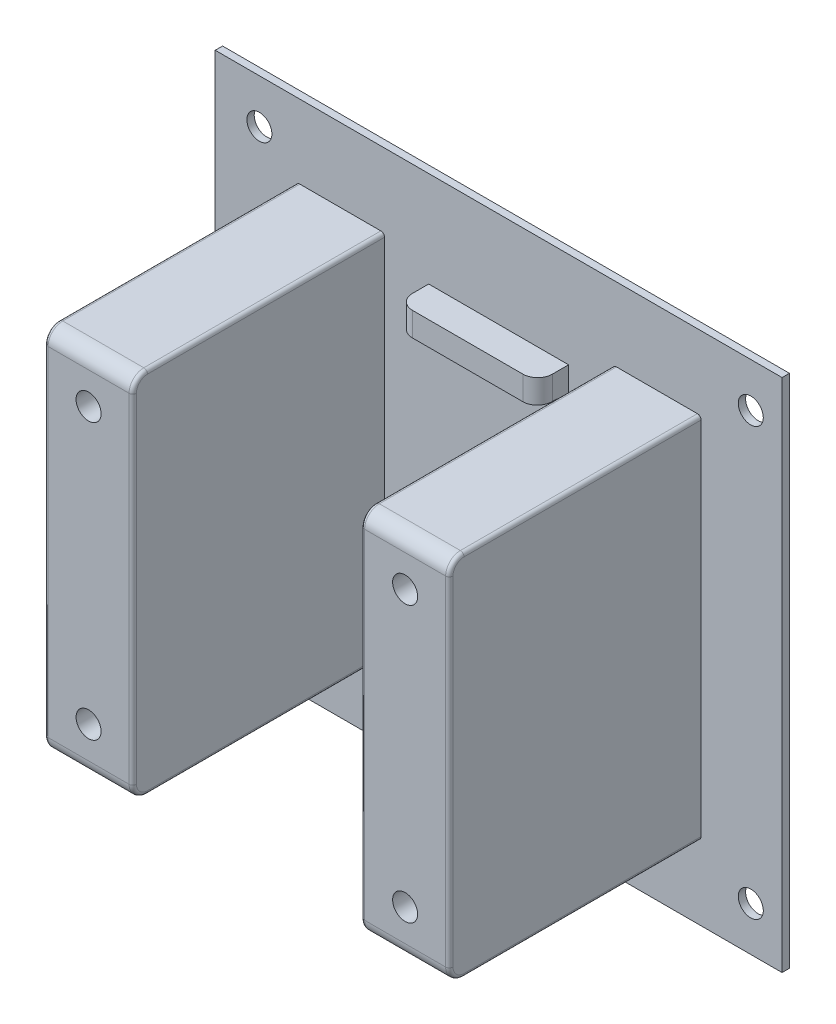
SolidWorks part; units mm, degrees
ref_plane "Front Plane" through (0, 0, 0) normal (1, 0, 0) x (0, 1, 0)
ref_plane "Bottom Plane" through (0, 0, 0) normal (0, 0, 1) x (0, 1, 0)
ref_plane "Right Plane" through (0, 0, 0) normal (0, 1, 0) x (-1, 0, 0)
ref_plane "Base Cut" through (0, 0, 7) normal (0, 0, 1) x (0, 1, 0)
sketch "Structural screws w/o heads" plane through (0, 0, 0) normal (0, 0, 1) x (0, 1, 0)
  line L1 (-19.42, -19.42) -> (19.42, -19.42) construction
  line L2 (-19.42, -19.42) -> (-19.42, 19.42) construction
  line L3 (-19.42, 19.42) -> (19.42, 19.42) construction
  line L4 (19.42, -19.42) -> (19.42, 19.42) construction
  line L5 (-19.42, -19.42) -> (19.42, 19.42) construction
  line L6 (-19.42, 19.42) -> (19.42, -19.42) construction
  circle A0 centre (-19.42, 19.42) radius 1.65 construction
  circle A1 centre (-19.42, -19.42) radius 1.65 construction
  circle A2 centre (19.42, 19.42) radius 1.65 construction
  circle A3 centre (19.42, -19.42) radius 1.65 construction
  circle A4 centre (0, 10.32) radius 1.65 construction
  circle A5 centre (0, -10.32) radius 1.65 construction
  point P0 (0, 0)
  dimension "D3" = 3.3
  dimension "D4" = 3.3
  dimension "D5" = 3.3
  dimension "D6" = 3.3
  dimension "D7" = 3.3
  dimension "D8" = 10.32
  dimension "D9" = 3.3
  dimension "D10" = 10.32
  dimension "D11" = 9.1
  dimension "D12" = 9.1
  dimension "D1" = 38.84
  dimension "D2" = 38.84
sketch "Sketch6" plane through (0, 0, 0) normal (0, 0, 1) x (0, 1, 0)
  line L0 (-30, -26.5) -> (-30, -31.5)
  line L1 (-30, 26.5) -> (30, 26.5)
  line L2 (-30, 26.5) -> (-30, -26.5)
  line L4 (30, 26.5) -> (30, -26.5)
  line L5 (-30, 26.5) -> (30, -26.5) construction
  line L6 (-30, -26.5) -> (30, 26.5) construction
  line L7 (30, -26.5) -> (30, -31.5)
  line L8 (-30, -31.5) -> (30, -31.5)
  point P0 (0, 0)
  dimension "D1" = 60
  dimension "D2" = 53
  dimension "D3" = 5
  dimension "D4" = 53
extrude "Mount Base" add sketch "Sketch6" along normal blind 10 separate body
sketch "Sketch 8" plane through (0, 0, 7) normal (0, 0, 1) x (0, 1, 0)
  line L1 (-19, 15.5) -> (19, 15.5)
  line L2 (-19, 15.5) -> (-19, -15.5)
  line L3 (-19, -15.5) -> (19, -15.5)
  line L4 (19, 15.5) -> (19, -15.5)
  line L5 (-19, 15.5) -> (19, -15.5) construction
  line L6 (-19, -15.5) -> (19, 15.5) construction
  point P0 (0, 0)
  dimension "D1" = 38
  dimension "D2" = 31
extrude "Cut-Base" cut sketch "Sketch 8" along normal blind 34
ref_plane "Bend Surface Plane" through (0, 0, 10) normal (0, 0, 1) x (0, 1, 0)
sketch "Sketch10" plane through (0, 0, 10) normal (0, 0, 1) x (0, 1, 0)
  line L0 (19, 0) -> (-19, 0) construction
  line L1 (-19, -15.5) -> (-19, 15.5) construction
  line L2 (0, 15.5) -> (0, -15.5) construction
  line L3 (-19, 15.5) -> (-22, 15.5)
  line L4 (-19, 15.5) -> (-19, -15.5)
  line L5 (-19, -15.5) -> (-22, -15.5)
  line L6 (-22, 15.5) -> (-22, -15.5)
  line L7 (19, -15.5) -> (-19, -15.5) construction
  line L8 (19, -15.5) -> (22, -15.5)
  line L9 (22, 15.5) -> (22, -15.5)
  line L10 (19, 15.5) -> (22, 15.5)
  line L11 (19, 15.5) -> (19, -15.5)
  point P6 (0, 0)
  point P17 (0, 0)
  dimension "D1" = 31
  dimension "D2" = 3
extrude "Bend Sides" add sketch "Sketch10" along normal blind 34.2
sketch "E-stop" plane through (0, 0, 10) normal (0, 0, 1) x (0, 1, 0)
  line L1 (-18.195, 14.995) -> (18.195, 14.995)
  line L2 (-18.195, 14.995) -> (-18.195, -14.995)
  line L3 (-18.195, -14.995) -> (18.195, -14.995)
  line L4 (18.195, 14.995) -> (18.195, -14.995)
  line L5 (-18.195, 14.995) -> (18.195, -14.995) construction
  line L6 (-18.195, -14.995) -> (18.195, 14.995) construction
  point P0 (0, 0)
  dimension "D1" = 36.39
  dimension "D2" = 29.99
ref_plane "Plane6" through (0, 0, 44.2) normal (0, 0, 1) x (1, 0, 0)
sketch "Sketch16" plane through (0, 0, 10) normal (0, 0, 1) x (0, 1, 0)
  line L0 (-22, 0) -> (22, 0) construction
  line L1 (-22, -15.5) -> (22, -15.5)
  line L2 (-22, -15.5) -> (-22, -18.5)
  line L3 (-22, -18.5) -> (22, -18.5)
  line L4 (22, -15.5) -> (22, -18.5)
  line L5 (22, -15.5) -> (22, 15.5) construction
  line L6 (-22, 18.5) -> (22, 18.5)
  line L7 (22, 15.5) -> (22, 18.5)
  line L8 (-22, 15.5) -> (22, 15.5)
  line L9 (-22, 15.5) -> (-22, 18.5)
  point P11 (0, 0)
  dimension "D1" = 44
  dimension "D2" = 3
extrude "Wire Sides" add sketch "Sketch16" along normal blind 34.2
ref_plane "Wire Holes Plane" through (0, 0, 44.2) normal (0, 0, 1) x (1, 0, 0)
draft "Draft9" type of draft neutral plane draft angle 1 faces to draft 1 face at (0, -19, 25.6) neutral plane through (0, 0, 0) neutral plane normal (0, 0, -1) parameters "D1"=1
draft "Draft10" type of draft neutral plane draft angle 1 faces to draft 1 face at (0, 19, 25.6) neutral plane through (0, 0, 0) neutral plane normal (0, 0, -1) parameters "D1"=1
sketch "Sketch20" plane through (0, 0, 0) normal (0, 0, 1) x (0, 1, 0)
  line L0 (0, 0) -> (0, 25) construction
  line L2 (-30, 26.5) -> (-30, 37)
  line L3 (-30, 37) -> (30, 37)
  line L4 (30, 27) -> (30, 37)
  line L5 (-30, 0) -> (30, 0) construction
  line L10 (0, 30.5) -> (0, -30.5) construction
  line L11 (0, -30.5) -> (-30, -28.4968) construction
  line L12 (0, -30.5) -> (30, -28.4968) construction
  line L13 (0, 30.5) -> (30, 28.4968) construction
  line L14 (0, 30.5) -> (-30, 28.4968) construction
  line L15 (-30, -37) -> (30, -37)
  line L16 (30, 27) -> (30, -37)
  line L18 (-30, 26.5) -> (-30, -37)
  point P11 (0, 0)
  point P19 (0, 0)
  dimension "D1" = 10
  dimension "D2" = 60
  dimension "D3" = 37
  dimension "D4" = 30.0668
  dimension "D5" = 30.4322
  dimension "D6" = 172.36
ref_plane "Plane8" through (0, 0, -3.18) normal (0, 0, 1) x (0, 1, 0)
extrude "Differential Clamp" add sketch "Sketch20" against normal blind 8.6 and the other way blind 10
sketch "Sketch22" plane through (0, 0, 0) normal (0, 0, 1) x (0, 1, 0)
  line L2 (-86.9562, -24.6938) -> (0, -30.5)
  line L7 (-30, 37) -> (30, 37)
  line L9 (-30, 37) -> (-86.9562, 37)
  line L10 (-86.9562, 37) -> (-86.9562, -24.6938)
  line L11 (0, -30.5) -> (0, 37) construction
  line L12 (86.9562, -24.6938) -> (0, -30.5)
  line L13 (30, 37) -> (86.9562, 37)
  line L14 (86.9562, 37) -> (86.9562, -24.6938)
  point P20 (0, 0)
  dimension "D1" = 61.6938
  dimension "D2" = 87.1498
extrude "Differential Bar cut" cut sketch "Sketch22" against normal blind 3.6 contours L2 L12 L14 L13 L7 L9 L10
ref_plane "Plane9" through (0, 0, -8.6) normal (0, 0, -1) x (-1, 0, 0)
sketch "Sketch 7" plane through (0, 0, 0) normal (0, 0, 1) x (0, 1, 0)
  line L0 (-22.42, 37.1638) -> (-22.42, -19.42)
  line L2 (-22.42, 37.1638) -> (-16.42, 37.1638)
  line L3 (-16.42, 37.1638) -> (-16.42, -19.42)
  line L4 (16.42, -19.42) -> (16.42, 37.1612)
  line L5 (-3, 37.1612) -> (3, 37.1612)
  line L6 (22.42, 37.1612) -> (22.42, -19.42)
  line L11 (-3, -10.32) -> (-3, 37.1612)
  line L12 (3, -10.32) -> (3, 37.1612)
  line L13 (16.42, 37.1612) -> (22.42, 37.1612)
  arc A1 (-22.42, -19.42) -> (-16.42, -19.42) centre (-19.42, -19.42) ccw
  arc A3 (16.42, -19.42) -> (22.42, -19.42) centre (19.42, -19.42) ccw
  arc A5 (-3, -10.32) -> (3, -10.32) centre (0, -10.32) ccw
  dimension "D1" = 56.5838
  dimension "D2" = 6
  dimension "D3" = 6
  dimension "D4" = 56.5812
  dimension "D5" = 6
  dimension "D6" = 6
  dimension "D7" = 6
  dimension "D8" = 44.84
extrude "Structural Screw w/ heads" cut sketch "Sketch 7" along normal blind 5
ref_plane "Clamp Hole Plane" through (0, 0, 10) normal (0, 0, 1) x (0, 1, 0)
sketch "Sketch25" plane through (0, 0, 10) normal (0, 0, 1) x (1, 0, 0)
  line L0 (-37, -30) -> (-37, 30) construction
  line L1 (37, 30) -> (-37, 30) construction
  line L2 (37, 0) -> (-37, 0) construction
  line L3 (0, 30) -> (0, -30) construction
  line L4 (-37, -30) -> (37, -30) construction
  circle A0 centre (-32, 29) radius 1.7
  circle A1 centre (-32, -29) radius 1.7
  circle A2 centre (32, -29) radius 1.7
  circle A3 centre (32, 29) radius 1.7
  point P10 (0, 0)
  point P17 (0, 0)
  dimension "D1" = 3.4
  dimension "D2" = 5
  dimension "D3" = 1
extrude "Screw holes" cut sketch "Sketch25" against normal blind 24
ref_plane "Plane11" through (0, 0, -8.6) normal (0, 0, -1) x (-1, 0, 0)
sketch "Sketch27" plane through (0, 0, -8.6) normal (0, 0, -1) x (-1, 0, 0)
  line L0 (37, -30) -> (37, 30) construction
  line L1 (31.9351, 25.7097) -> (34.817, 27.2987)
  line L2 (34.817, 27.2987) -> (34.8819, 30.5889)
  line L3 (34.8819, 30.5889) -> (32.0649, 32.2903)
  line L4 (32.0649, 32.2903) -> (29.183, 30.7013)
  line L5 (29.183, 30.7013) -> (29.1181, 27.4111)
  line L6 (29.1181, 27.4111) -> (31.9351, 25.7097)
  line L7 (-37, -30) -> (-33.3748, -30) construction
  line L8 (28.7091, -29) -> (30.3546, -31.85)
  line L9 (30.3546, -31.85) -> (33.6454, -31.85)
  line L10 (33.6454, -31.85) -> (35.2909, -29)
  line L11 (35.2909, -29) -> (33.6454, -26.15)
  line L12 (33.6454, -26.15) -> (30.3546, -26.15)
  line L13 (30.3546, -26.15) -> (28.7091, -29)
  line L14 (0, 30) -> (0, -30) construction
  line L15 (-30.3546, -26.15) -> (-28.7091, -29)
  line L16 (-33.6454, -26.15) -> (-30.3546, -26.15)
  line L17 (-35.2909, -29) -> (-33.6454, -26.15)
  line L18 (-33.6454, -31.85) -> (-35.2909, -29)
  line L19 (-30.3546, -31.85) -> (-33.6454, -31.85)
  line L20 (-28.7091, -29) -> (-30.3546, -31.85)
  line L21 (-29.1181, 27.4111) -> (-31.9351, 25.7097)
  line L22 (-29.183, 30.7013) -> (-29.1181, 27.4111)
  line L23 (-32.0649, 32.2903) -> (-29.183, 30.7013)
  line L24 (-34.8819, 30.5889) -> (-32.0649, 32.2903)
  line L25 (-34.817, 27.2987) -> (-34.8819, 30.5889)
  line L26 (-31.9351, 25.7097) -> (-34.817, 27.2987)
  circle A0 centre (32, 29) radius 2.85 construction
  circle A1 centre (32, -29) radius 2.85 construction
  circle A2 centre (-32, -29) radius 2.85 construction
  circle A3 centre (-32, 29) radius 2.85 construction
  point P26 (0, 0)
  dimension "D3" = 5.7
  dimension "D1" = 5.7
  dimension "D2" = 1.13
  dimension "D4" = 1
extrude "Nut hole" cut sketch "Sketch27" against normal blind 2.6
fillet "Fillet7" radius 2 1 edges at (-37, 30, 5)
fillet "Fillet8" radius 2 1 edges at (-37, -30, 5)
fillet "Fillet9" radius 2 1 edges at (-37, 30, -6.1)
fillet "Fillet10" radius 2 1 edges at (-37, -30, -6.1)
fillet "Fillet15" radius 2 2 edges at (0, 18.8254, 10) (0, -18.8254, 10)
ref_plane "Sectional Left Plane" through (0, 22, 0) normal (0, 1, 0) x (1, 0, 0)
ref_plane "Sectional Right Plane" through (0, -22, 0) normal (0, -1, 0) x (-1, 0, 0)
ref_plane "Plane13" through (0, 0, 9) normal (0, 0, 1) x (1, 0, 0)
sketch "Sketch41" plane through (0, 0, 9) normal (0, 0, 1) x (1, 0, 0)
  line L1 (37.5468, -30.066) -> (-37.5468, -30.066)
  line L2 (37.5468, -30.066) -> (37.5468, 30.066)
  line L3 (37.5468, 30.066) -> (-37.5468, 30.066)
  line L4 (-37.5468, -30.066) -> (-37.5468, 30.066)
  line L5 (37.5468, -30.066) -> (-37.5468, 30.066) construction
  line L6 (37.5468, 30.066) -> (-37.5468, -30.066) construction
  point P0 (0, 0)
  dimension "D1" = 60.132
  dimension "D2" = 75.0936
ref_plane "Plane15" through (0, 0, -8.6) normal (0, 0, -1) x (-1, 0, 0)
sketch "Sketch42" plane through (0, 0, -8.6) normal (0, 0, 1) x (1, 0, 0)
  line L0 (0, 23) -> (0, -23) construction
  line L1 (37, 35) -> (-37, 35)
  line L2 (37, 35) -> (37, -35)
  line L3 (37, -35) -> (-37, -35)
  line L4 (-37, 35) -> (-37, 23)
  line L5 (37, 35) -> (-37, -35) construction
  line L6 (37, -35) -> (-37, 35) construction
  line L7 (37, 0) -> (28.5, 0) construction
  line L8 (28.5, 23) -> (28.5, -23)
  line L9 (28.5, 23) -> (-37, 23)
  line L10 (28.5, -23) -> (-37, -23)
  line L11 (-37, -23) -> (-37, -35)
  point P0 (0, 0)
  point P9 (0, 0)
  point P14 (28.5, 0)
  point P17 (0, 23)
  point P20 (0, -23)
  dimension "D1" = 74
  dimension "D2" = 46
  dimension "D3" = 70
  dimension "D4" = 65.5
  dimension "D5" = 46
  dimension "D6" = 12
extrude "Boss-Extrude1" add sketch "Sketch42" along normal blind 17.6
ref_plane "Plane16" through (0, 0, 0) normal (0, 0, -1) x (-1, 0, 0)
sketch "Sketch43" plane through (0, 0, 0) normal (0, 0, -1) x (-1, 0, 0)
  line L0 (-24.6938, 86.9562) -> (37, 86.9562)
  line L1 (37, 86.9562) -> (37, -86.9562)
  line L2 (37, -86.9562) -> (-24.6938, -86.9562)
  line L3 (-24.6938, -86.9562) -> (-30.5, 0)
  line L4 (-30.5, 0) -> (-24.6938, 86.9562)
extrude "Cut-Extrude6" cut sketch "Sketch43" along normal blind 8.6
sketch "Sketch45" plane through (0, 0, 0) normal (0, 0, -1) x (-1, 0, 0)
  line L0 (37, 23) -> (-28.5, 23)
  line L1 (-28.5, 23) -> (-28.5, -23)
  line L2 (-28.5, -23) -> (37, -23)
  line L3 (37, -23) -> (37, 23)
ref_plane "Plane17" through (0, 0, -8.6) normal (0, 0, -1) x (-1, 0, 0)
ref_plane "Plane18" through (0, 0, 9) normal (0, 0, 1) x (1, 0, 0)
sketch "Sketch48" plane through (0, 0, 9) normal (0, 0, 1) x (1, 0, 0)
  line L1 (-37, 35) -> (37, 35)
  line L2 (-37, 35) -> (-37, -35)
  line L3 (-37, -35) -> (37, -35)
  line L4 (37, 35) -> (37, -35)
extrude "Cut-Extrude9" cut sketch "Sketch48" against normal blind 17.6
sketch "Sketch49" plane through (0, 0, 9) normal (0, 0, 1) x (1, 0, 0)
  line L1 (38.5, -35) -> (-38.5, -35)
  line L2 (38.5, -35) -> (38.5, 35)
  line L3 (38.5, 35) -> (-38.5, 35)
  line L4 (-38.5, -35) -> (-38.5, 35)
  line L5 (38.5, -35) -> (-38.5, 35) construction
  line L6 (38.5, 35) -> (-38.5, -35) construction
  point P0 (0, 0)
  dimension "D1" = 70
  dimension "D2" = 77
extrude "Boss-Extrude2" add sketch "Sketch49" along normal blind 1
sketch "Sketch50" plane through (0, 0, 9) normal (0, 0, 1) x (1, 0, 0)
  line L0 (-38.5, 29) -> (38.5, 29) construction
  line L1 (-38.5, 35) -> (-38.5, -35) construction
  line L2 (38.5, -35) -> (38.5, 35) construction
  line L3 (38.5, 35) -> (-38.5, 35) construction
  line L4 (37, 0) -> (-37, 0) construction
  line L5 (34.25, 29) -> (34.25, -29) construction
  line L7 (-32.5, 29) -> (-32.5, -29) construction
  line L8 (-38.5, -29) -> (38.5, -29) construction
  circle A0 centre (-32.5, 29) radius 1.7
  circle A1 centre (34.25, 29) radius 1.7
  circle A2 centre (34.25, -29) radius 1.7
  circle A3 centre (-32.5, -29) radius 1.7
  point P12 (0, 0)
  point P21 (34.25, 0)
  point P25 (-32.5, 0)
  dimension "D4" = 3.4
  dimension "D5" = 3.4
  dimension "D1" = 6
  dimension "D2" = 4.25
  dimension "D3" = 6
extrude "Cut-Extrude10" cut sketch "Sketch50" along normal blind 1
ref_plane "Plane20" through (0, 0, 10) normal (0, 0, 1) x (1, 0, 0)
ref_plane "Plane21" through (0, 0, 44.2) normal (0, 0, 1) x (1, 0, 0)
sketch "Sketch52" plane through (0, 0, 44.2) normal (0, 0, 1) x (1, 0, 0)
  line L0 (9.5, 0) -> (-9.5, 0) construction
  line L1 (15.5, 16.7902) -> (-15.5, 16.7902) construction
  line L3 (0, 8.1338) -> (0, -8.1338) construction
  line L13 (-15.5, 24.2285) -> (-9.5, 24.2285)
  line L16 (-9.5, 24.2285) -> (-9.5, 18.2285)
  line L29 (-15.5, 18.2285) -> (-15.5, 24.2285)
  line L31 (-18.5, 22) -> (-18.5, -22) construction
  line L55 (-15.5, 18.2285) -> (-15.5, 16.7902)
  line L56 (-15.5, 16.7902) -> (-9.5, 16.7902)
  line L57 (-9.5, 18.2285) -> (-9.5, 16.7902)
  line L58 (15.5, 18.2285) -> (15.5, 16.7902)
  line L59 (15.5, 16.7902) -> (9.5, 16.7902)
  line L60 (9.5, 18.2285) -> (9.5, 16.7902)
  line L61 (9.5, 24.2285) -> (9.5, 18.2285)
  line L62 (15.5, 24.2285) -> (9.5, 24.2285)
  line L63 (15.5, 18.2285) -> (15.5, 24.2285)
  line L64 (15.5, -18.2285) -> (15.5, -24.2285)
  line L65 (15.5, -24.2285) -> (9.5, -24.2285)
  line L66 (9.5, -24.2285) -> (9.5, -18.2285)
  line L67 (9.5, -18.2285) -> (9.5, -16.7902)
  line L68 (15.5, -16.7902) -> (9.5, -16.7902)
  line L69 (15.5, -18.2285) -> (15.5, -16.7902)
  line L70 (-15.5, -18.2285) -> (-15.5, -16.7902)
  line L71 (-15.5, -16.7902) -> (-9.5, -16.7902)
  line L72 (-9.5, -18.2285) -> (-9.5, -16.7902)
  line L73 (-9.5, -24.2285) -> (-9.5, -18.2285)
  line L74 (-15.5, -24.2285) -> (-9.5, -24.2285)
  line L75 (-15.5, -18.2285) -> (-15.5, -24.2285)
  point P3 (0, 0)
  point P15 (0, 0)
  point P23 (0, 0)
  dimension "D1" = 6
  dimension "D2" = 6
  dimension "D3" = 7.4383
  dimension "D4" = 3
extrude "Cut-Extrude12" cut sketch "Sketch52" against normal blind 34.2
ref_plane "Plane22" through (0, 0, 44.2) normal (0, 0, 1) x (1, 0, 0)
sketch "Sketch53" plane through (0, 0, 44.2) normal (0, 0, 1) x (1, 0, 0)
  line L0 (-15.5, -22) -> (-15.5, 22) construction
  line L1 (-9.5, -18.2285) -> (9.5, -18.2285)
  line L2 (-9.5, -18.2285) -> (-9.5, -24)
  line L3 (-9.5, -24) -> (9.5, -24)
  line L4 (9.5, -18.2285) -> (9.5, -24)
  line L5 (-9.5, 22) -> (9.5, 22)
  line L6 (-9.5, 22) -> (-9.5, 16.2285)
  line L7 (-9.5, 16.2285) -> (9.5, 16.2285)
  line L8 (9.5, 22) -> (9.5, 16.2285)
  line L12 (-38.5, -35) -> (38.5, -35) construction
  dimension "D1" = 19
  dimension "D2" = 19
  dimension "D3" = 5.7715
  dimension "D4" = 5.7715
  dimension "D5" = 6
  dimension "D6" = 11
extrude "Cut-Extrude13" cut sketch "Sketch53" against normal blind 30
fillet "Fillet17" radius 2 1 edges at (-9.5, -20.3761, 14.2)
ref_plane "Plane23" through (0, 0, 39.2) normal (0, 0, 1) x (1, 0, 0)
sketch "Sketch55" plane through (0, 0, 10) normal (0, 0, 1) x (1, 0, 0)
  line L0 (0, 15.8849) -> (0, -15.8849) construction
  line L2 (-18.5, 22) -> (-18.5, -22)
  line L4 (-27.5, 22) -> (-27.5, -22)
  line L10 (18.5, 22) -> (18.5, -22)
  line L12 (27.5, 22) -> (27.5, -22)
  line L14 (27.5, 0) -> (-27.5, 0) construction
  line L15 (-18.5, 22) -> (-15.5, 22)
  line L16 (-27.5, 22) -> (-27.5, 25)
  line L17 (-27.5, 25) -> (-15.5, 25)
  line L18 (-15.5, 22) -> (-15.5, 25)
  line L19 (-27.5, -25) -> (-15.5, -25)
  line L20 (-15.5, -22) -> (-15.5, -25)
  line L21 (-18.5, -22) -> (-15.5, -22)
  line L22 (-27.5, -22) -> (-27.5, -25)
  line L23 (18.5, -22) -> (15.5, -22)
  line L24 (15.5, -22) -> (15.5, -25)
  line L25 (27.5, -25) -> (15.5, -25)
  line L26 (27.5, -22) -> (27.5, -25)
  line L27 (27.5, 25) -> (15.5, 25)
  line L28 (15.5, 22) -> (15.5, 25)
  line L29 (18.5, 22) -> (15.5, 22)
  line L30 (27.5, 22) -> (27.5, 25)
  point P9 (0, 0)
  point P20 (0, 0)
  dimension "D1" = 12
  dimension "D2" = 9
  dimension "D3" = 3
  dimension "D4" = 3
extrude "Boss-Extrude3" add sketch "Sketch55" along normal blind 34.2
sketch "Sketch54" plane through (0, 0, 39.2) normal (0, 0, 1) x (1, 0, 0)
  line L0 (-15.5, -25) -> (-15.5, 25) construction
  line L1 (24.4, 20.3593) -> (24.4, 17.0107)
  line L2 (0, 14.185) -> (0, 23.185) construction
  line L3 (15, 18.2) -> (-15, 18.2) construction
  line L4 (15, 18.2) -> (15, -18.2) construction
  line L5 (15, -18.2) -> (-15, -18.2) construction
  line L6 (-15, 18.2) -> (-15, -18.2) construction
  line L7 (15, 18.2) -> (-15, -18.2) construction
  line L8 (15, -18.2) -> (-15, 18.2) construction
  line L10 (-21.5, 22) -> (-21.5, -22) construction
  line L11 (-15.5, 22) -> (-27.5, 22) construction
  line L12 (-27.5, -22) -> (-15.5, -22) construction
  line L15 (21.5, 18.685) -> (-21.5, 18.685) construction
  line L16 (21.5, 22.0336) -> (24.4, 20.3593)
  line L17 (-24.4, 17.0107) -> (-21.5, 15.3364)
  line L18 (-21.5, 15.3364) -> (-18.6, 17.0107)
  line L19 (-18.6, 17.0107) -> (-18.6, 20.3593)
  line L20 (-18.6, 20.3593) -> (-21.5, 22.0336)
  line L21 (-21.5, 22.0336) -> (-24.4, 20.3593)
  line L22 (-24.4, 20.3593) -> (-24.4, 17.0107)
  line L23 (18.6, 20.3593) -> (21.5, 22.0336)
  line L24 (18.6, 17.0107) -> (18.6, 20.3593)
  line L25 (21.5, 15.3364) -> (18.6, 17.0107)
  line L26 (24.4, 17.0107) -> (21.5, 15.3364)
  line L27 (14.185, 0) -> (-14.185, 0) construction
  line L28 (21.5, -22.0336) -> (24.4, -20.3593)
  line L29 (18.6, -20.3593) -> (21.5, -22.0336)
  line L30 (18.6, -17.0107) -> (18.6, -20.3593)
  line L31 (21.5, -15.3364) -> (18.6, -17.0107)
  line L32 (24.4, -17.0107) -> (21.5, -15.3364)
  line L33 (24.4, -20.3593) -> (24.4, -17.0107)
  line L34 (-24.4, -20.3593) -> (-24.4, -17.0107)
  line L35 (-21.5, -22.0336) -> (-24.4, -20.3593)
  line L36 (-18.6, -20.3593) -> (-21.5, -22.0336)
  line L37 (-18.6, -17.0107) -> (-18.6, -20.3593)
  line L38 (-21.5, -15.3364) -> (-18.6, -17.0107)
  line L39 (-24.4, -17.0107) -> (-21.5, -15.3364)
  circle A0 centre (0, 0) radius 14.185 construction
  circle A1 centre (-21.5, 18.685) radius 2.9 construction
  circle A2 centre (21.5, 18.685) radius 2.9 construction
  circle A3 centre (21.5, -18.685) radius 2.9 construction
  circle A4 centre (-21.5, -18.685) radius 2.9 construction
  point P12 (0, 18.685)
  point P25 (0, 18.685)
  point P44 (0, 0)
  dimension "D1" = 28.37
  dimension "D2" = 30
  dimension "D5" = 5.8
  dimension "D3" = 36.4
  dimension "D4" = 9
  dimension "D6" = 0
extrude "Cut-Extrude14" cut sketch "Sketch54" along normal blind 2.6
sketch "Sketch56" plane through (0, 0, 44.2) normal (0, 0, 1) x (1, 0, 0)
  line L0 (13.2137, 0) -> (-13.2137, 0) construction
  line L1 (14.185, 0) -> (-14.185, 0) construction
  line L2 (0, 9.8869) -> (0, -9.8869) construction
  circle A0 centre (-21.5, 18.685) radius 1.7
  circle A1 centre (21.5, 18.685) radius 1.7
  circle A2 centre (21.5, -18.685) radius 1.7
  circle A3 centre (-21.5, -18.685) radius 1.7
  point P9 (0, 0)
  point P13 (0, 0)
  dimension "D1" = 3.4
extrude "Cut-Extrude15" cut sketch "Sketch56" against normal blind 8
fillet "Fillet18" radius 2 7 edges at (9.5, -20.3761, 14.2) (9.5, 20.3761, 14.2) (-9.5, 20.3761, 14.2) (-21.5, 25, 44.2) (-21.5, -25, 44.2) (21.5, -25, 44.2) (21.5, 25, 44.2)
fillet "Fillet20" radius 0.5 20 edges at (27.5, -25, 26.1) (27.5, -24.4142, 43.6142) (27.5, 25, 26.1) (27.5, 24.4142, 43.6142) (15.5, 25, 26.1) (15.5, 24.4142, 43.6142) (15.5, -25, 26.1) (15.5, -24.4142, 43.6142) (-15.5, -25, 26.1) (-15.5, -24.4142, 43.6142) (-15.5, 25, 26.1) (-15.5, 24.4142, 43.6142) (-27.5, 25, 26.1) (-27.5, 24.4142, 43.6142) (-27.5, -25, 26.1) (-27.5, -24.4142, 43.6142) (27.5, 0, 44.2) (15.5, 0, 44.2) (-15.5, 0, 44.2) (-27.5, 0, 44.2)
